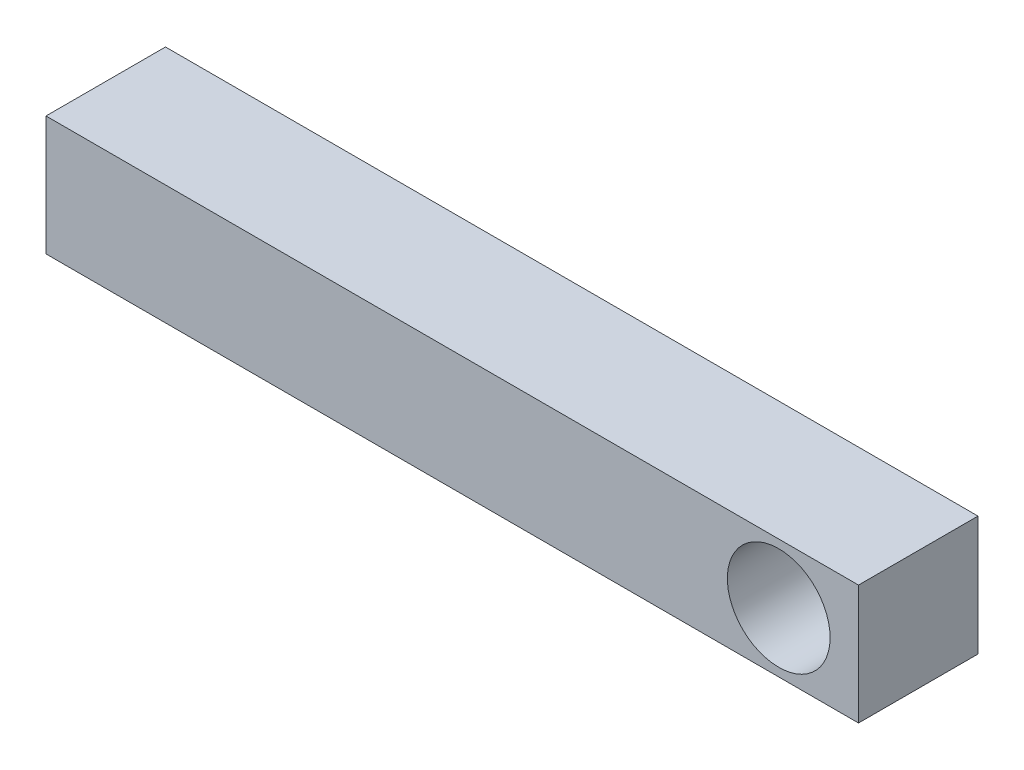
SolidWorks part; units mm, degrees
ref_plane "前视基准面" through (0, 0, 0) normal (0, 0, 1) x (1, 0, 0)
ref_plane "上视基准面" through (0, 0, 0) normal (0, 1, 0) x (1, 0, 0)
ref_plane "右视基准面" through (0, 0, 0) normal (1, 0, 0) x (0, 0, -1)
sketch "草图1" plane through (0, 0, 0) normal (0, 0, 1) x (1, 0, 0)
  line L1 (-17, 2.5) -> (17, 2.5)
  line L2 (-17, 2.5) -> (-17, -2.5)
  line L3 (-17, -2.5) -> (17, -2.5)
  line L4 (17, 2.5) -> (17, -2.5)
  dimension "D1" = 17
  dimension "D2" = 17
  dimension "D3" = 5
  dimension "D4" = 2.5
extrude "凸台-拉伸1" add sketch "草图1" along normal blind 5
sketch "草图2" plane through (0, 0, 5) normal (0, 0, 1) x (1, 0, 0)
  circle A0 centre (13.6616, 0) radius 2.1498
extrude "切除-拉伸1" cut sketch "草图2" against normal blind 5
